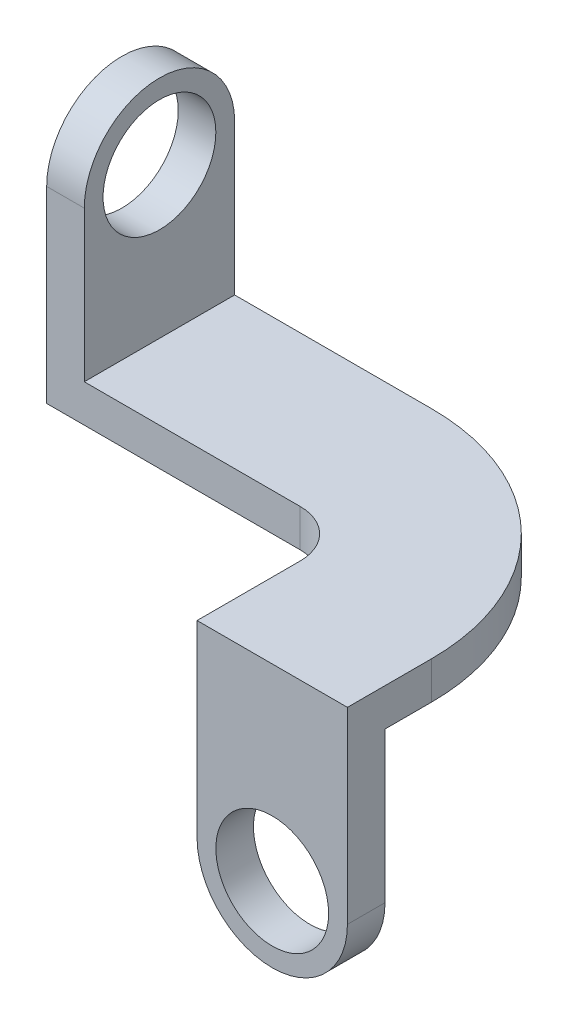
SolidWorks part; units mm, degrees
ref_plane "Alzado" through (0, 0, 0) normal (0, 0, 1) x (1, 0, 0)
ref_plane "Planta" through (0, 0, 0) normal (0, 1, 0) x (1, 0, 0)
ref_plane "Vista lateral" through (0, 0, 0) normal (1, 0, 0) x (0, 0, -1)
sketch "Croquis1" plane through (0, 0, 0) normal (0, 1, 0) x (1, 0, 0)
  line L0 (0, 0) -> (0, 101.6)
  line L1 (0, 101.6) -> (158.496, 101.6)
  line L2 (304.8, -44.704) -> (304.8, -101.6)
  line L3 (304.8, -101.6) -> (203.2, -101.6)
  line L4 (203.2, -101.6) -> (203.2, -32.004)
  line L5 (171.196, 0) -> (0, 0)
  arc A0 (203.2, -32.004) -> (171.196, 0) centre (171.196, -32.004) ccw
  arc A1 (158.496, 101.6) -> (304.8, -44.704) centre (158.496, -44.704) cw
  point P11 (304.8, 101.6)
  dimension "D3" = 32.004
  dimension "D4" = 146.304
  dimension "D1" = 101.6
  dimension "D2" = 304.8
  dimension "D5" = 203.2
  dimension "D6" = 101.6
extrude "Saliente-Extruir1" add sketch "Croquis1" along normal blind 25.4
sketch "Croquis2" plane through (0, 0, 0) normal (0, -1, 0) x (1, 0, 0)
  line L0 (304.8, 101.6) -> (304.8, 44.704) construction
  line L1 (203.2, 101.6) -> (304.8, 101.6)
  line L2 (203.2, 101.6) -> (203.2, 76.2)
  line L3 (203.2, 76.2) -> (304.8, 76.2)
  line L4 (304.8, 101.6) -> (304.8, 76.2)
  dimension "D1" = 25.4
extrude "Saliente-Extruir2" add sketch "Croquis2" along normal blind 101.6
sketch "Croquis3" plane through (0, 0, 101.6) normal (0, 0, 1) x (1, 0, 0)
  line L0 (304.8, -101.6) -> (203.2, -101.6) construction
  circle A0 centre (254, -101.6) radius 50.8
  dimension "D1" = 101.6
extrude "Saliente-Extruir3" add sketch "Croquis3" against normal blind 25.4
sketch "Croquis4" plane through (0, 0, 101.6) normal (0, 0, 1) x (1, 0, 0)
  circle A0 centre (254, -101.6) radius 38.1
  dimension "D1" = 76.2
extrude "Cortar-Extruir1" cut sketch "Croquis4" against normal through all
sketch "Croquis5" plane through (0, 25.4, 0) normal (0, 1, 0) x (1, 0, 0)
  line L0 (158.496, 101.6) -> (0, 101.6) construction
  line L1 (0, 0) -> (25.4, 0)
  line L2 (0, 0) -> (0, 101.6)
  line L3 (0, 101.6) -> (25.4, 101.6)
  line L4 (25.4, 0) -> (25.4, 101.6)
  dimension "D1" = 25.4
extrude "Saliente-Extruir4" add sketch "Croquis5" along normal blind 101.6
sketch "Croquis6" plane through (25.4, 0, 0) normal (1, 0, 0) x (0, 0, -1)
  line L0 (0, 127) -> (101.6, 127) construction
  circle A0 centre (50.8, 127) radius 50.8
  dimension "D1" = 101.6
extrude "Saliente-Extruir5" add sketch "Croquis6" against normal blind 25.4
sketch "Croquis7" plane through (25.4, 0, 0) normal (1, 0, 0) x (0, 0, -1)
  circle A0 centre (50.8, 127) radius 38.1
  dimension "D1" = 76.2
extrude "Cortar-Extruir3" cut sketch "Croquis7" against normal through all
